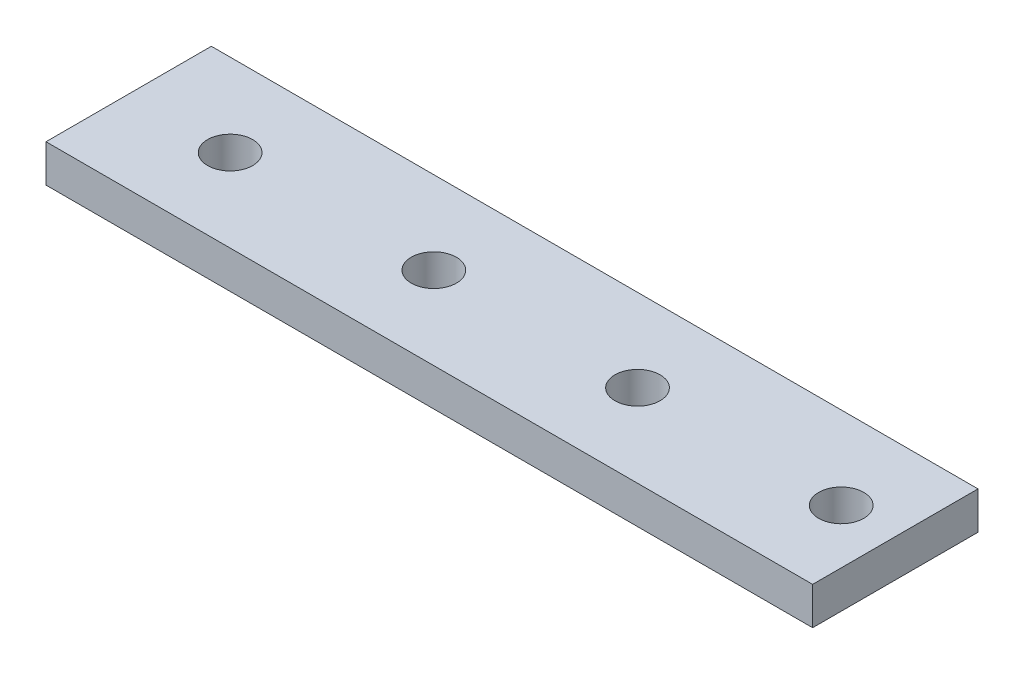
SolidWorks part; units mm, degrees
ref_plane "Front Plane" through (0, 0, 0) normal (0, 0, 1) x (1, 0, 0)
ref_plane "Top Plane" through (0, 0, 0) normal (0, 1, 0) x (1, 0, 0)
ref_plane "Right Plane" through (0, 0, 0) normal (1, 0, 0) x (0, 0, -1)
sketch "Sketch1" plane through (0, 0, 0) normal (0, 1, 0) x (1, 0, 0)
  line L1 (-51, -11) -> (51, -11)
  line L2 (-51, -11) -> (-51, 11)
  line L3 (-51, 11) -> (51, 11)
  line L4 (51, -11) -> (51, 11)
  line L5 (-51, -11) -> (51, 11) construction
  line L6 (-51, 11) -> (51, -11) construction
  circle A0 centre (-37.5, 0) radius 3
  circle A1 centre (-10.4, 0) radius 3
  circle A2 centre (16.7, 0) radius 3
  circle A3 centre (43.8, 0) radius 3
  point P0 (0, 0)
  point P6 (-37.5, 0)
  point P8 (43.8, 0)
  dimension "D5" = 6
  dimension "D1" = 102
  dimension "D2" = 22
  dimension "D3" = 13.5
  dimension "D4" = 7.2
  dimension "D6" = 4
extrude "Boss-Extrude1" add sketch "Sketch1" along normal blind 5
ref_plane "Plane1" through (0, 2.5, 0) normal (0, 1, 0) x (1, 0, 0)
sketch "Sketch2" plane through (0, 2.5, 0) normal (0, 1, 0) x (1, 0, 0)
  point P0 (-37.5, 0)
  point P1 (43.8, 0)
